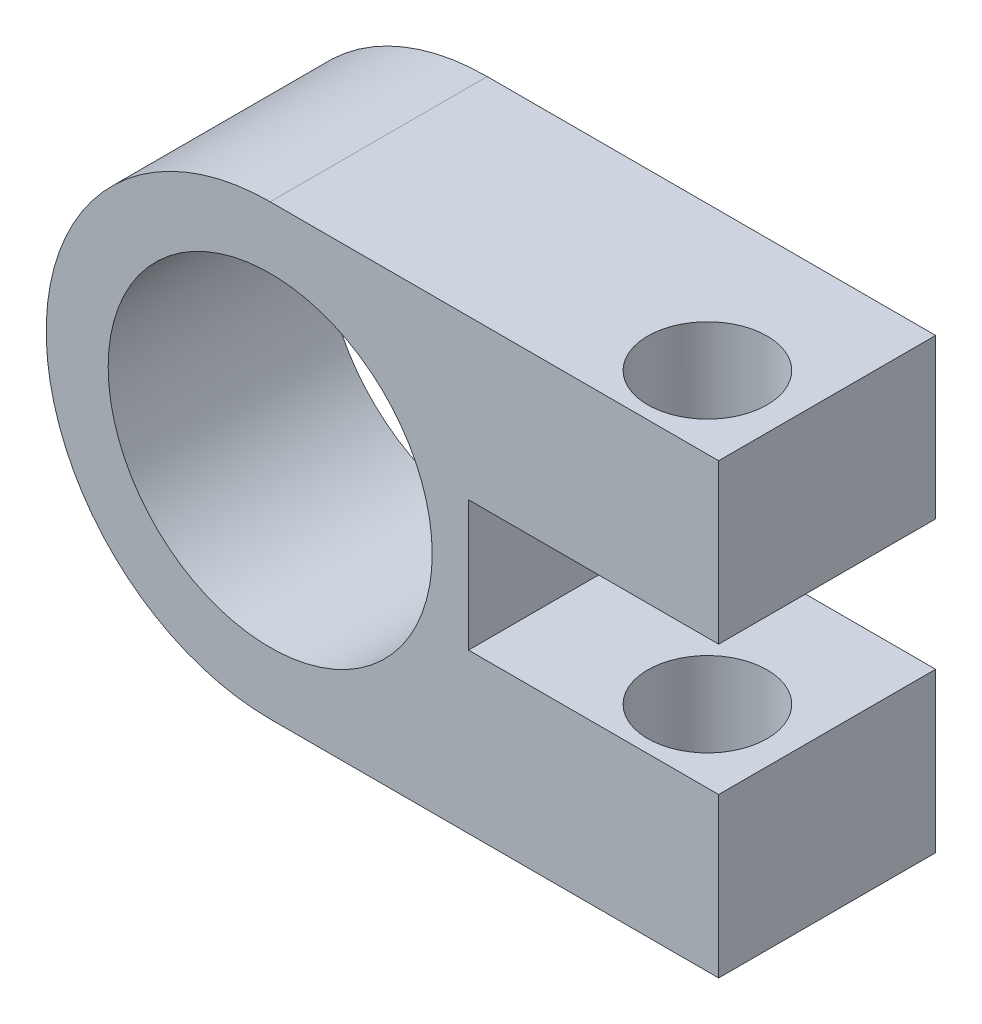
SolidWorks part; units mm, degrees
ref_plane "Front Plane" through (0, 0, 0) normal (0, 0, 1) x (1, 0, 0)
ref_plane "Top Plane" through (0, 0, 0) normal (0, 1, 0) x (1, 0, 0)
ref_plane "Right Plane" through (0, 0, 0) normal (1, 0, 0) x (0, 0, -1)
sketch "Sketch1" plane through (0, 0, 0) normal (0, 0, 1) x (1, 0, 0)
  line L0 (0, 15.4836) -> (31, 15.4836)
  line L1 (0, -15.4836) -> (31, -15.4836)
  line L2 (31, -15.4836) -> (31, 15.4836)
  circle A0 centre (0, 0) radius 11.2
  arc A1 (0, 15.4836) -> (0, -15.4836) centre (0, 0) ccw
  dimension "D1" = 22.4
  dimension "D2" = 31
extrude "Boss-Extrude1" add sketch "Sketch1" along normal blind 15
sketch "Sketch2" plane through (0, -15.4836, 0) normal (0, -1, 0) x (1, 0, 0)
  circle A0 centre (25.208, 9.9829) radius 4.125
  dimension "D1" = 8.25
extrude "Cut-Extrude1" cut sketch "Sketch2" against normal blind 38 contours A0
sketch "Sketch4" plane through (0, -15.4836, 0) normal (0, -1, 0) x (1, 0, 0)
  line L0 (25.208, 14.1079) -> (25.208, 15) construction
  line L1 (0, 15) -> (31, 15) construction
  circle A0 centre (25.208, 9.9829) radius 4.125 construction
sketch "Sketch6" plane through (0, 0, 15) normal (0, 0, 1) x (1, 0, 0)
  line L0 (0, 0) -> (31, 0) construction
  line L1 (31, -15.4836) -> (31, 15.4836) construction
sketch "Sketch7" plane through (0, 0, 15) normal (0, 0, 1) x (1, 0, 0)
  line L0 (25.4581, -15.4836) -> (25.4581, 15.4836) construction
  line L1 (0, -15.4836) -> (31, -15.4836) construction
  line L2 (31, 15.4836) -> (0, 15.4836) construction
  line L3 (25.4581, 4.5) -> (13.7081, 4.5)
  line L4 (13.7081, 4.5) -> (13.7081, -4.5)
  line L6 (0, 0) -> (31, 0) construction
  line L7 (13.7081, -4.5) -> (31, -4.5)
  line L8 (31, -15.4836) -> (31, 15.4836) construction
  line L9 (25.4581, 4.5) -> (31, 4.5)
  line L10 (31, 4.5) -> (31, -4.5)
  line L11 (31, -4.5) -> (34.9671, -4.3788)
  point P8 (13.7081, 0)
  dimension "D1" = 11.75
  dimension "D2" = 9
extrude "Cut-Extrude2" cut sketch "Sketch7" against normal blind 38 contours L7 L4 L3 L9 L10
